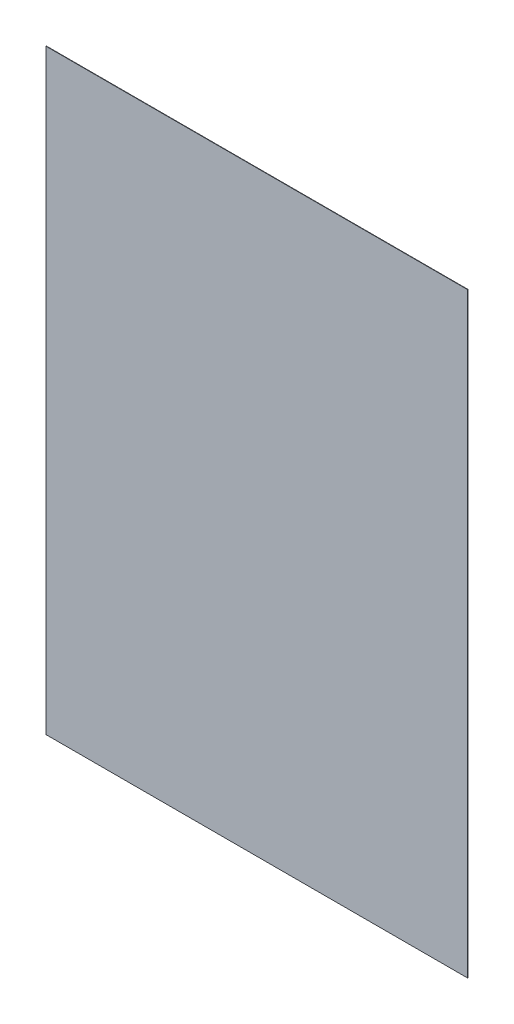
SolidWorks part; units mm, degrees
material "Papier ondulé"
ref_plane "Face" through (0, 0, 0) normal (0, 0, 1) x (1, 0, 0)
ref_plane "Dessus" through (0, 0, 0) normal (0, 1, 0) x (1, 0, 0)
ref_plane "Droite" through (0, 0, 0) normal (1, 0, 0) x (0, 0, -1)
sketch "Esquisse1" plane through (0, 0, 0) normal (0, 0, 1) x (1, 0, 0)
  line L1 (-105, -148.5) -> (105, -148.5)
  line L2 (-105, -148.5) -> (-105, 148.5)
  line L3 (-105, 148.5) -> (105, 148.5)
  line L4 (105, -148.5) -> (105, 148.5)
  line L5 (-105, -148.5) -> (105, 148.5) construction
  line L6 (-105, 148.5) -> (105, -148.5) construction
  point P0 (0, 0)
  dimension "D1" = 210
  dimension "D2" = 297
extrude "Boss.-Extru.1" add sketch "Esquisse1" along normal blind 0.2
